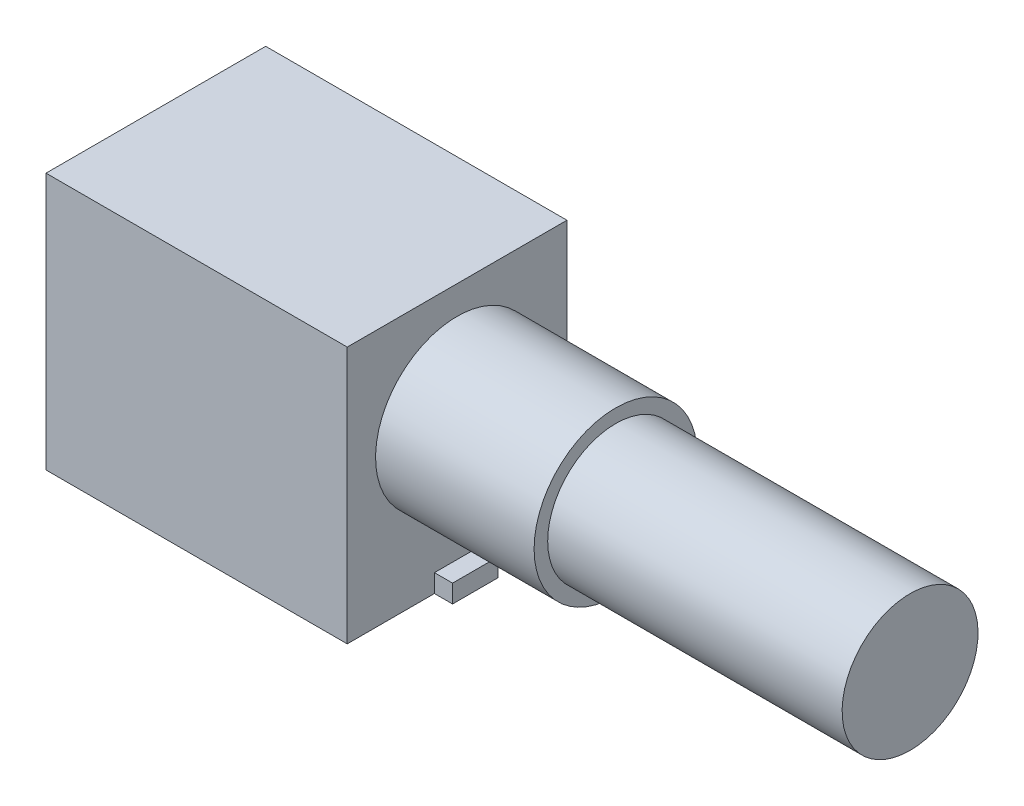
SolidWorks part; units mm, degrees
ref_plane "Front Plane" through (0, 0, 0) normal (0, 0, 1) x (1, 0, 0)
ref_plane "Top Plane" through (0, 0, 0) normal (0, 1, 0) x (1, 0, 0)
ref_plane "Right Plane" through (0, 0, 0) normal (1, 0, 0) x (0, 0, -1)
sketch "Sketch1" plane through (0, 0, 0) normal (0, 0, 1) x (1, 0, 0)
  line L1 (0, 0) -> (13.3, 0)
  line L2 (0, 0) -> (0, 11.35)
  line L3 (0, 11.35) -> (13.3, 11.35)
  line L4 (13.3, 0) -> (13.3, 11.35)
  dimension "D1" = 13.3
  dimension "D2" = 11.35
extrude "Boss-Extrude1" add sketch "Sketch1" along normal blind 9.7
sketch "Sketch2" plane through (13.3, 0, 0) normal (1, 0, 0) x (0, 0, -1)
  line L0 (-9.7, 0) -> (0, 0) construction
  circle A0 centre (-4.85, 6.5) radius 3.6
  dimension "D2" = 7.2
  dimension "D1" = 6.5
extrude "Boss-Extrude2" add sketch "Sketch2" along normal blind 7
sketch "Sketch3" plane through (20.3, 0, 0) normal (1, 0, 0) x (0, 0, -1)
  circle A0 centre (-4.85, 6.5) radius 3
  dimension "D1" = 6
extrude "Boss-Extrude4" add sketch "Sketch3" along normal offset from surface (13 mm away) 20 up to face at (13.3, 5.675, 4.85) offset beyond the face yes
sketch "Sketch4" plane through (13.3, 0, 0) normal (1, 0, 0) x (0, 0, -1)
  line L0 (-9.7, 0) -> (0, 0) construction
  line L1 (-5.85, 0) -> (-3.85, 0)
  line L2 (-5.85, 0) -> (-5.85, 0.8)
  line L3 (-5.85, 0.8) -> (-3.85, 0.8)
  line L4 (-3.85, 0) -> (-3.85, 0.8)
  point P6 (-4.85, 0.8)
  point P7 (-4.85, 0)
  dimension "D1" = 2
  dimension "D2" = 0.8
extrude "Boss-Extrude5" add sketch "Sketch4" along normal blind 0.8
ref_plane "Plane1" through (0, 0, 4.85) normal (0, 0, 1) x (1, 0, 0)
